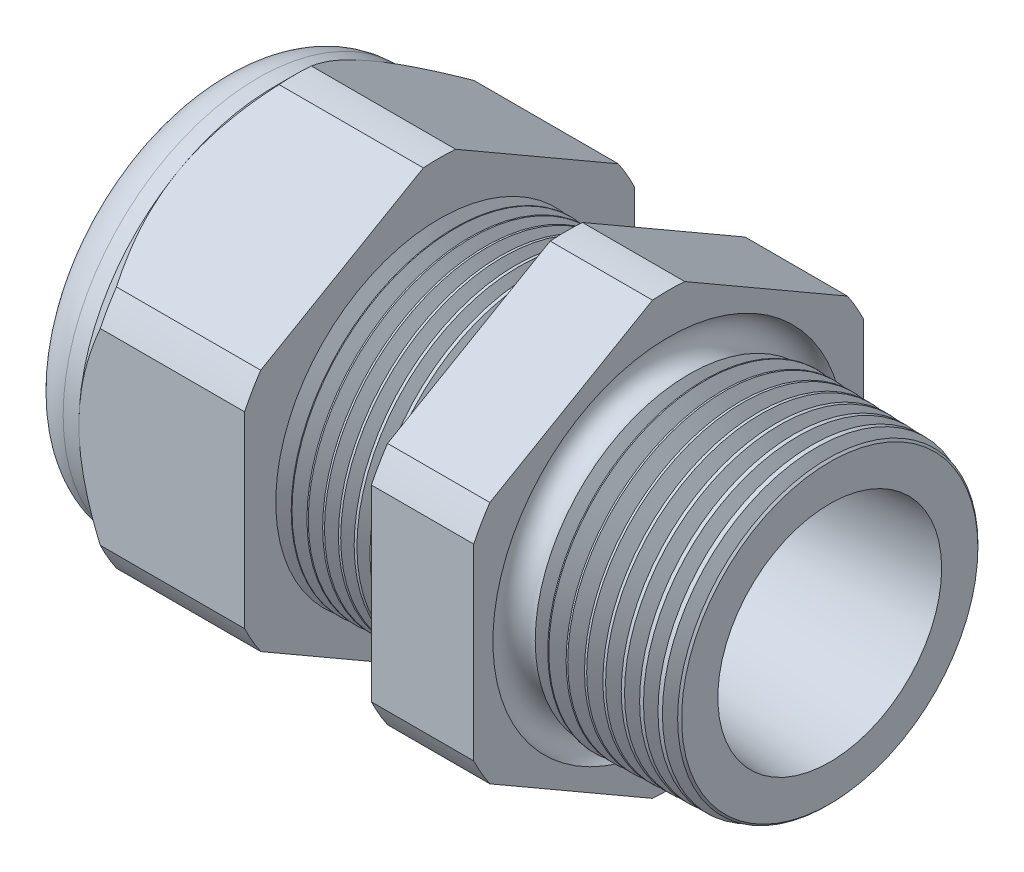
SolidWorks part; units mm, degrees
ref_plane "Front Plane" through (0, 0, 0) normal (0, 0, 1) x (1, 0, 0)
ref_plane "Top Plane" through (0, 0, 0) normal (0, 1, 0) x (1, 0, 0)
ref_plane "Right Plane" through (0, 0, 0) normal (1, 0, 0) x (0, 0, -1)
sketch "Sketch10" plane through (0, 0, 0) normal (0, 0, 1) x (1, 0, 0)
  line L0 (0, 0) -> (-115.3565, 0) construction
  line L1 (-29.972, 3.937) -> (-19.072, 3.937)
  line L2 (0, 5.4696) -> (0, 7.5016)
  line L3 (-7.874, 7.7078) -> (0, 7.5016)
  line L4 (-7.874, 19.05) -> (-7.874, 7.7078)
  line L5 (-7.874, 19.05) -> (-12.874, 19.05)
  line L6 (-12.874, 19.05) -> (-12.874, 7.8387)
  line L7 (-19.072, 8.001) -> (-12.874, 7.8387)
  line L8 (-19.072, 8.001) -> (-19.072, 19.05)
  line L9 (-19.072, 19.05) -> (-27.172, 19.05)
  line L10 (-27.172, 19.05) -> (-27.172, 9.525)
  line L11 (-27.172, 9.525) -> (-29.972, 9.525)
  line L12 (-29.972, 9.525) -> (-29.972, 3.937)
  line L13 (-19.072, 3.937) -> (0, 5.4696)
  dimension "D1" = 29.972
  dimension "D2" = 7.874
  dimension "D3" = 1.5
  dimension "D4" = 2.032
  dimension "A" = 16.002
  dimension "D6" = 19.05
  dimension "D8" = 38.1
  dimension "D9" = 2.8
  dimension "D10" = 8.1
  dimension "D11" = 5
  dimension "D" = 7.874
revolve "Revolve2" add sketch "Sketch10" angle 360 about L0
sketch "Sketch12" plane through (-27.172, 0, 0) normal (-1, 0, 0) x (0, 0, 1)
  line L1 (-0.7885, 10.5433) -> (-8.7365, 5.9545)
  line L2 (-9.525, 4.5888) -> (-9.525, -4.5888)
  line L3 (-8.7365, -5.9545) -> (-0.7885, -10.5433)
  line L4 (0.7885, -10.5433) -> (8.7365, -5.9545)
  line L5 (9.525, -4.5888) -> (9.525, 4.5888)
  line L6 (8.7365, 5.9545) -> (0.7885, 10.5433)
  circle A0 centre (0, 0) radius 9.525 construction
  arc A1 (0.7885, 10.5433) -> (-0.7885, 10.5433) centre (0, 0) ccw
  arc A2 (-8.7365, 5.9545) -> (-9.525, 4.5888) centre (0, 0) ccw
  arc A3 (-9.525, -4.5888) -> (-8.7365, -5.9545) centre (0, 0) ccw
  arc A4 (-0.7885, -10.5433) -> (0.7885, -10.5433) centre (0, 0) ccw
  arc A5 (8.7365, -5.9545) -> (9.525, -4.5888) centre (0, 0) ccw
  arc A6 (9.525, 4.5888) -> (8.7365, 5.9545) centre (0, 0) ccw
  dimension "D2" = 21.1455
  dimension "D1" = 19.05
extrude "Cut-Extrude2" cut sketch "Sketch12" against normal through all flip side to cut
fillet "Fillet4" radius 2.032 1 edges at (-29.972, 0, -9.525)
sketch "Sketch19" plane through (-27.172, 0, 0) normal (-1, 0, 0) x (0, 0, 1)
  line L0 (9.525, 0) -> (9.525, 4.5888) construction
  circle A0 centre (0, 0) radius 9.525
extrude "Cut-Extrude3" cut sketch "Sketch19" against normal blind 2 draft 45 flip side to cut
chamfer "Chamfer1" distance 0.254 angle 45 1 edges at (0, 0, -7.5016)
sketch "Sketch21" plane through (-29.972, 0, 0) normal (-1, 0, 0) x (0, 0, 1)
  circle A0 centre (0, 0) radius 3.937
  circle A2 centre (0, 0) radius 3.937 construction
extrude "plug" add sketch "Sketch21" against normal blind 3.81 separate body
sketch "Sketch22" plane through (-29.972, 0, 0) normal (-1, 0, 0) x (0, 0, 1)
  circle A0 centre (0, 0) radius 3.683
  circle A1 centre (0, 0) radius 3.937 construction
  dimension "D1" = 0.254
extrude "Cut-Extrude4" cut sketch "Sketch22" against normal blind 0.508
sketch "Sketch27" plane through (-29.464, 0, 0) normal (-1, 0, 0) x (0, 0, 1)
  line L0 (-4.3624, 0) -> (4.3624, 0) construction
  circle A0 centre (-2.918, 0) radius 0.762
  circle A1 centre (0, 0) radius 3.683 construction
  dimension "D1" = 0.003
  dimension "holedia" = 1.524
extrude "plugholes" cut sketch "Sketch27" against normal through all
pattern_circular "CirPattern1" count 3 over 360 about axis through (0, 0, 0) along (1, 0, 0) of "plugholes"
sketch "Sketch28" plane through (-29.464, 0, 0) normal (-1, 0, 0) x (0, 0, 1)
  circle A0 centre (0, 0) radius 0.762
  dimension "midholedia" = 1.524
extrude "midhole" cut sketch "Sketch28" against normal through all
sketch "Sketch29" plane through (0, 0, 0) normal (0, 0, 1) x (1, 0, 0)
  line L0 (-19.072, 8.001) -> (-18.339, 7.9818)
  line L1 (-12.874, 7.8387) -> (-19.072, 8.001) construction
  line L2 (-18.339, 7.9818) -> (-18.7221, 7.3566)
  line L3 (-18.7221, 7.3566) -> (-19.072, 8.001)
  dimension "D1" = 60
  dimension "D2" = 60
  dimension "D3" = 0.635
revolve "Cut-Revolve1" cut sketch "Sketch29" angle 360 about axis through (0, 0, 0) along (-1, 0, 0)
pattern_linear "LPattern1" count 8 spacing 0.762 along (1, 0, 0) of "Cut-Revolve1"
sketch "Sketch30" plane through (0, 0, 0) normal (0, 0, 1) x (1, 0, 0)
  line L0 (-7.874, 7.7078) -> (-6.9944, 7.6847)
  line L1 (-7.874, 10.5433) -> (-7.874, 5.9545) construction
  line L2 (-0.2539, 7.5082) -> (-7.874, 7.7078) construction
  line L3 (-6.9944, 7.6847) -> (-7.4542, 6.9345)
  line L4 (-7.4542, 6.9345) -> (-7.874, 7.7078)
  dimension "D1" = 60
  dimension "D2" = 60
  dimension "D3" = 0.762
revolve "Cut-Revolve2" cut sketch "Sketch30" angle 360 about axis through (0, 0, 0) along (-1, 0, 0)
pattern_linear "LPattern2" count 9 spacing 0.889 along (1, 0, 0) of "Cut-Revolve2"
sketch "Sketch31" [suppressed] plane through (-38.354, 0, 0) normal (-1, 0, 0) x (0, 0, 1)
  line L0 (-1.905, 1.905) -> (1.905, 1.905)
  line L1 (-1.905, -1.905) -> (1.905, -1.905)
  circle A0 centre (0, 0) radius 1.905 construction
  arc A1 (-1.905, 1.905) -> (-1.905, -1.905) centre (-1.905, 0) ccw
  arc A2 (1.905, 1.905) -> (1.905, -1.905) centre (1.905, 0) cw
extrude "Cut-Extrude5" [suppressed] cut sketch "Sketch31" against normal through all
sketch "Sketch32" plane through (0, 0, 0) normal (0, 0, 1) x (1, 0, 0)
  line L0 (-7.874, 10.5433) -> (-7.874, 5.9545) construction
  circle A0 centre (-7.747, 7.7078) radius 0.889
  dimension "D2" = 1.778
  dimension "D1" = 0.127
revolve "Cut-Revolve3" cut sketch "Sketch32" angle 360 about axis through (0, 0, 0) along (-1, 0, 0)
